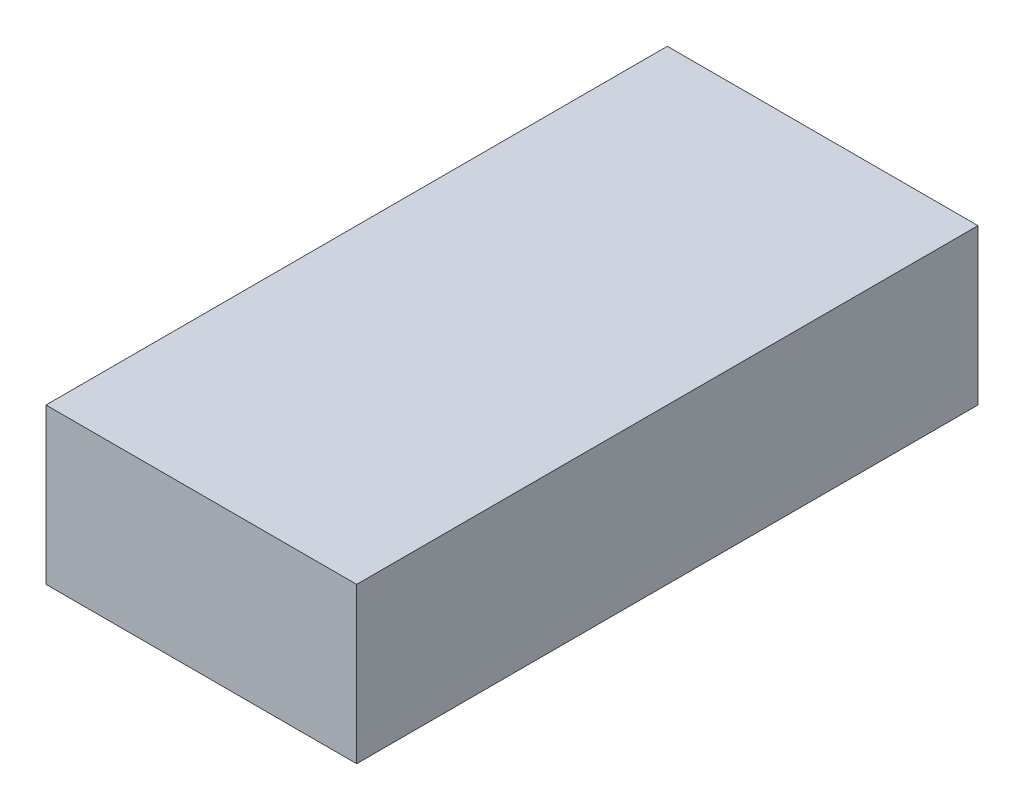
SolidWorks part; units mm, degrees
material "Gray Cast Iron"
ref_plane "Front Plane" through (0, 0, 0) normal (0, 0, 1) x (1, 0, 0)
ref_plane "Top Plane" through (0, 0, 0) normal (0, 1, 0) x (1, 0, 0)
ref_plane "Right Plane" through (0, 0, 0) normal (1, 0, 0) x (0, 0, -1)
sketch "Sketch1" plane through (0, 0, 0) normal (0, 1, 0) x (1, 0, 0)
  line L1 (-50.152, 82.67) -> (-0.152, 82.67)
  line L2 (-50.152, 82.67) -> (-50.152, -17.33)
  line L3 (-50.152, -17.33) -> (-0.152, -17.33)
  line L4 (-0.152, 82.67) -> (-0.152, -17.33)
  dimension "D1" = 0.152
  dimension "D2" = 50.152
  dimension "D3" = 82.67
  dimension "D4" = 17.33
extrude "Boss-Extrude1" add sketch "Sketch1" along normal blind 25
